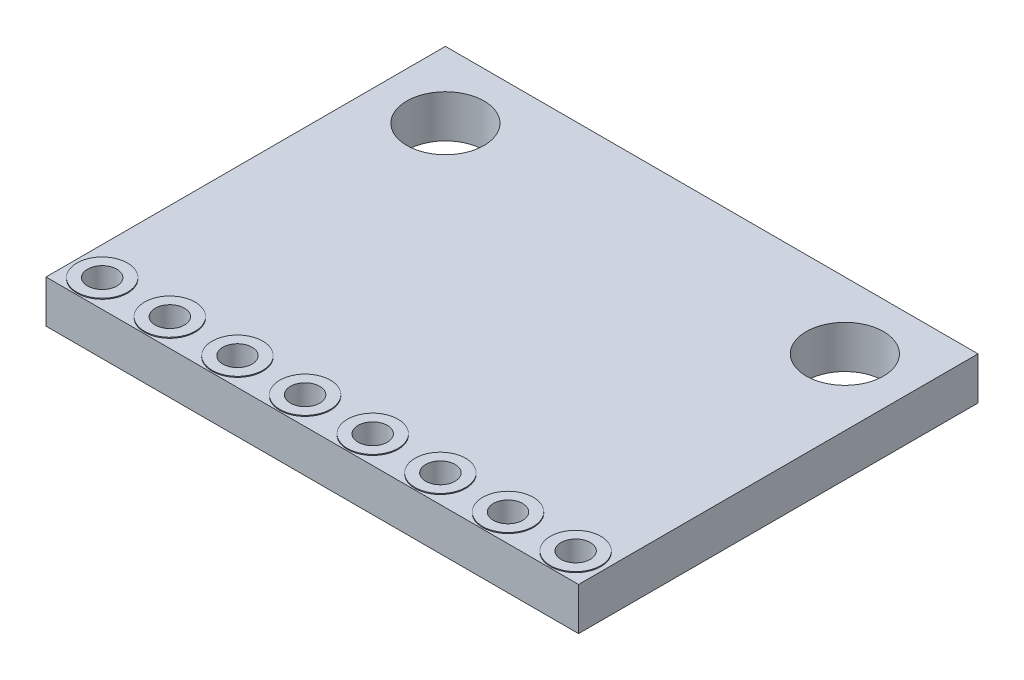
SolidWorks part; units mm, degrees
ref_plane "Plano frontal" through (0, 0, 0) normal (0, 0, 1) x (1, 0, 0)
ref_plane "Plano superior" through (0, 0, 0) normal (0, 1, 0) x (1, 0, 0)
ref_plane "Plano direito" through (0, 0, 0) normal (1, 0, 0) x (0, 0, -1)
sketch "Esboço1" plane through (0, 0, 0) normal (0, 1, 0) x (1, 0, 0)
  line L0 (0, -7.5) -> (0, 7.5) construction
  line L1 (-10, 7.5) -> (10, 7.5)
  line L2 (-10, 7.5) -> (-10, -7.5)
  line L3 (-10, -7.5) -> (10, -7.5)
  line L4 (10, 7.5) -> (10, -7.5)
  line L5 (-10, 7.5) -> (10, -7.5) construction
  line L6 (-10, -7.5) -> (10, 7.5) construction
  circle A0 centre (-7.5, 5) radius 1.45
  circle A1 centre (7.5, 5) radius 1.45
  circle A2 centre (-1.27, -6.5) radius 0.55
  circle A3 centre (-3.81, -6.5) radius 0.55
  circle A4 centre (-6.35, -6.5) radius 0.55
  circle A5 centre (-8.89, -6.5) radius 0.55
  circle A6 centre (1.27, -6.5) radius 0.55
  circle A7 centre (3.81, -6.5) radius 0.55
  circle A8 centre (6.35, -6.5) radius 0.55
  circle A9 centre (8.89, -6.5) radius 0.55
  point P0 (0, 0)
  dimension "D5" = 2.9
  dimension "D6" = 1.1
  dimension "D8" = 1.27
  dimension "D1" = 20
  dimension "D2" = 15
  dimension "D3" = 2.5
  dimension "D4" = 2.5
  dimension "D7" = 1
  dimension "D9" = 4
  dimension "D10" = 5
extrude "Ressalto-extrusão1" add sketch "Esboço1" along normal blind 1.6
sketch "Esboço2" plane through (0, 1.6, 0) normal (0, 1, 0) x (1, 0, 0)
  circle A57 centre (-6.35, -6.5) radius 0.95
  circle A58 centre (-8.89, -6.5) radius 0.95
  circle A59 centre (-8.89, -6.5) radius 0.95
  circle A60 centre (-3.81, -6.5) radius 0.95
  circle A61 centre (-1.27, -6.5) radius 0.95
  circle A62 centre (1.27, -6.5) radius 0.95
  circle A63 centre (3.81, -6.5) radius 0.95
  circle A64 centre (6.35, -6.5) radius 0.95
  circle A65 centre (8.89, -6.5) radius 0.95
  circle A66 centre (-8.89, -6.5) radius 0.55 construction
  circle A67 centre (-8.89, -6.5) radius 0.55
  circle A68 centre (-6.35, -6.5) radius 0.55
  circle A69 centre (-3.81, -6.5) radius 0.55
  circle A70 centre (-1.27, -6.5) radius 0.55
  circle A71 centre (1.27, -6.5) radius 0.55
  circle A72 centre (3.81, -6.5) radius 0.55
  circle A73 centre (6.35, -6.5) radius 0.55
  circle A74 centre (8.89, -6.5) radius 0.55
  dimension "D1" = 0.4
  dimension "D2" = 8
  dimension "D3" = 8
extrude "Ressalto-extrusão2" add sketch "Esboço2" along normal blind 0.035
sketch "Esboço3" plane through (0, 0, 0) normal (0, -1, 0) x (1, 0, 0)
  circle A0 centre (8.89, 6.5) radius 0.55 construction
  circle A1 centre (8.89, 6.5) radius 0.55
  circle A2 centre (8.89, 6.5) radius 0.95
  circle A3 centre (6.35, 6.5) radius 0.55
  circle A4 centre (6.35, 6.5) radius 0.95
  circle A5 centre (3.81, 6.5) radius 0.55
  circle A6 centre (3.81, 6.5) radius 0.95
  circle A7 centre (1.27, 6.5) radius 0.55
  circle A8 centre (1.27, 6.5) radius 0.95
  circle A9 centre (-1.27, 6.5) radius 0.55
  circle A10 centre (-1.27, 6.5) radius 0.95
  circle A11 centre (-3.81, 6.5) radius 0.55
  circle A12 centre (-3.81, 6.5) radius 0.95
  circle A13 centre (-6.35, 6.5) radius 0.55
  circle A14 centre (-6.35, 6.5) radius 0.95
  circle A15 centre (-8.89, 6.5) radius 0.55
  circle A16 centre (-8.89, 6.5) radius 0.95
  dimension "D1" = 0.4
  dimension "D2" = 8
extrude "Ressalto-extrusão3" add sketch "Esboço3" along normal blind 0.035
